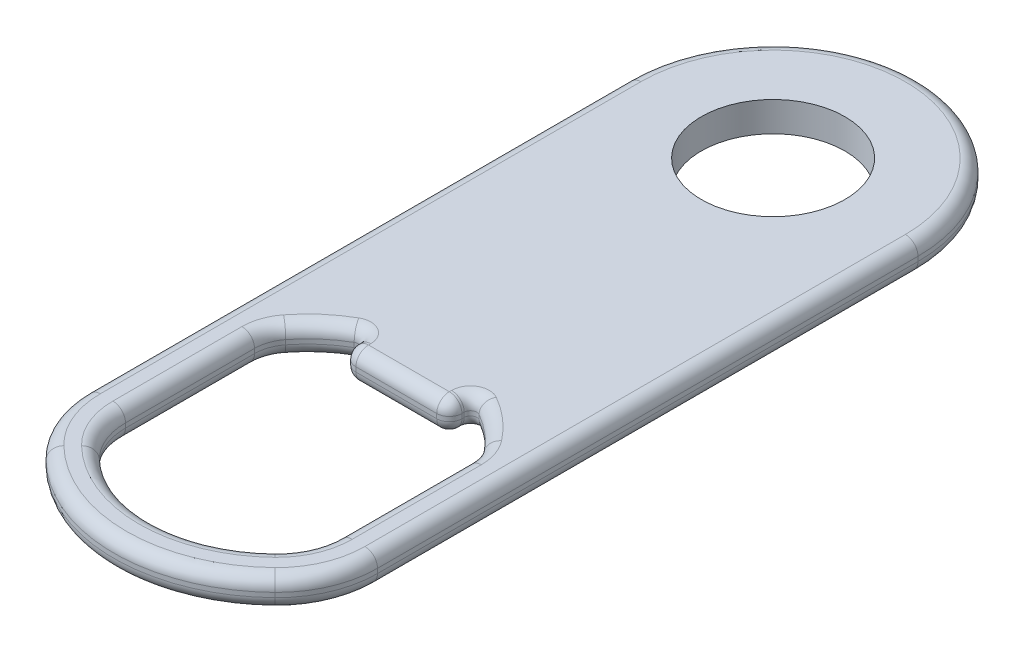
SolidWorks part; units mm, degrees
ref_plane "Front Plane" through (0, 0, 0) normal (0, 0, 1) x (1, 0, 0)
ref_plane "Top Plane" through (0, 0, 0) normal (0, 1, 0) x (1, 0, 0)
ref_plane "Right Plane" through (0, 0, 0) normal (1, 0, 0) x (0, 0, -1)
sketch "Sketch2" plane through (0, 0, 0) normal (1, 0, 0) x (0, 0, -1)
  line L1 (6.5, 3) -> (-6.5, 3) construction
  line L3 (6.5, 10.92) -> (-6.5, 10.92)
  line L4 (10.5, 10.92) -> (0, 10.92) construction
ref_plane "Plane1" through (0, 10.92, 0) normal (0, -1, 0) x (0, 0, 1)
sketch "Sketch3" plane through (0, 10.92, 0) normal (0, -1, 0) x (0, 0, 1)
  line L0 (-5.7, 0) -> (-12, 0)
  line L6 (49.3226, 0) -> (52.3226, 0)
  line L10 (0, 0) -> (0, 20.1636) construction
  line L14 (-12, 0) -> (-12, 11.5)
  line L15 (-12, 0) -> (52.3226, 0) construction
  line L19 (29.9066, 4.2079) -> (29.9066, 0)
  line L20 (27.9066, 4.2079) -> (29.9066, 4.2079)
  line L21 (31.7328, 8.5) -> (44.6183, 8.5)
  line L23 (-12, 11.5) -> (45.4063, 11.5)
  line L24 (5.7, 0) -> (29.9066, 0)
  circle A3 centre (0, 0) radius 5 construction
  arc A4 (5.7, 0) -> (-5.7, 0) centre (0, 0) ccw
  circle A6 centre (0, 0) radius 5.7 construction
  arc A7 (31.7328, 8.5) -> (27.9066, 4.2079) centre (36.9473, 0.0001) ccw
  arc A8 (44.6183, 8.5) -> (49.3226, 0) centre (39.2913, 0) cw
  arc A9 (45.4063, 11.5) -> (52.3226, 0) centre (39.3036, 0) cw
  dimension "D2" = 11.5
  dimension "D3" = 3
  dimension "D1" = 0.7
extrude "Boss-Extrude1" add sketch "Sketch3" against normal blind 2.36
sketch "Sketch5" plane through (0, 10.92, 0) normal (0, -1, 0) x (0, 0, 1)
  line L0 (45.4063, 11.5) -> (-12, 11.5) construction
  line L3 (0, 11.5) -> (0, 20.0815)
  line L4 (0, 20.0815) -> (-17.2066, 20.0815)
  line L5 (-17.2066, 20.0815) -> (-17.2066, -3.3259)
  line L6 (-17.2066, -3.3259) -> (-11.0086, -3.3259)
  arc A0 (0, 11.5) -> (-11.0086, -3.3259) centre (0, 0) ccw
  arc A1 (5.7, 0) -> (-5.7, 0) centre (0, 0) ccw construction
extrude "Cut-Extrude1" cut sketch "Sketch5" against normal blind 10
fillet "Fillet1" radius 1 1 edges at (-4.2079, 12.1, 29.9066)
fillet "Fillet2" radius 8 1 edges at (-11.5, 12.1, 45.4063)
fillet "Fillet3" radius 5 1 edges at (-8.5, 12.1, 44.6183)
fillet "Fillet4" radius 3 1 edges at (-8.5, 12.1, 31.7328)
fillet "Fillet5" radius 0.5 1 edges at (-4.2079, 12.1, 27.9066)
fillet "Fillet6" radius 1 8 edges at (-4.8997, 10.92, 51.3654) (-10.8699, 10.92, 46.0128) (-8.1317, 10.92, -8.1317) (-4.8997, 13.28, 51.3654) (-10.8699, 13.28, 46.0128) (-8.1317, 13.28, -8.1317) (-11.5, 10.92, 21.4504) (-11.5, 13.28, 21.4504)
fillet "Fillet7" radius 1 18 edges at (-3.7642, 10.92, 48.5895) (-8.1039, 10.92, 44.8562) (-8.5, 10.92, 37.7841) (-8.3372, 10.92, 31.6878) (-6.5346, 10.92, 29.4147) (-4.4571, 10.92, 28.2956) (-4.2079, 10.92, 28.8174) (-3.915, 10.92, 29.6137) (-3.7642, 13.28, 48.5895) (-8.1039, 13.28, 44.8562) (-8.5, 13.28, 37.7841) (-8.3372, 13.28, 31.6878) (-6.5346, 13.28, 29.4147) (-4.4571, 13.28, 28.2956) (-4.2079, 13.28, 28.8174) (-3.915, 13.28, 29.6137) (-1.6039, 10.92, 29.9066) (-1.6039, 13.28, 29.9066)
mirror "Mirror1" about plane through (0, 0, 0) normal (1, 0, 0) of bodies 104 101
sketch "Sketch6" plane through (0, 13.28, 0) normal (0, 1, 0) x (1, 0, 0)
  line L0 (17.8459, 0) -> (-16.8237, 0) construction
  line L1 (0, 20.7291) -> (0, 0) construction
  line L2 (9.517, 0) -> (13.311, 0) construction
  line L3 (9.1928, 2.4632) -> (12.8575, 3.4452) construction
  line L6 (9.517, 0) -> (9.1928, 2.4632) construction
  line L7 (9.3549, 1.2316) -> (-9.4356, -1.2422) construction
  line L8 (0, 0) -> (-2.1225, 16.1223) construction
  line L9 (-9.1928, -2.4632) -> (-9.517, 0)
  line L10 (-9.517, 0) -> (-13.311, 0)
  line L11 (-9.1928, -2.4632) -> (-12.8575, -3.4452)
  arc A1 (13.6022, -0.6813) -> (12.811, 0) centre (12.811, -0.8) ccw construction
  arc A2 (13.311, 0) -> (12.8575, 3.4452) centre (0, 0) ccw construction
  arc A3 (12.8, 0) -> (12, -0.8) centre (12.8, -0.8) ccw construction
  circle A4 centre (0, 0) radius 12.811 construction
  arc A5 (9.517, 0) -> (-9.4356, -1.2422) centre (0, 0) ccw construction
  circle A6 centre (0, 0) radius 13.311 construction
  arc A7 (-12.8575, -3.4452) -> (-13.311, 0) centre (0, 0) cw
  point P15 (-3.5196, 15.876)
  dimension "D1" = 15
  dimension "D2" = 0.5
extrude "Boss-Extrude2" [suppressed] add sketch "Sketch6" against normal up to surface (2.36 mm away)
